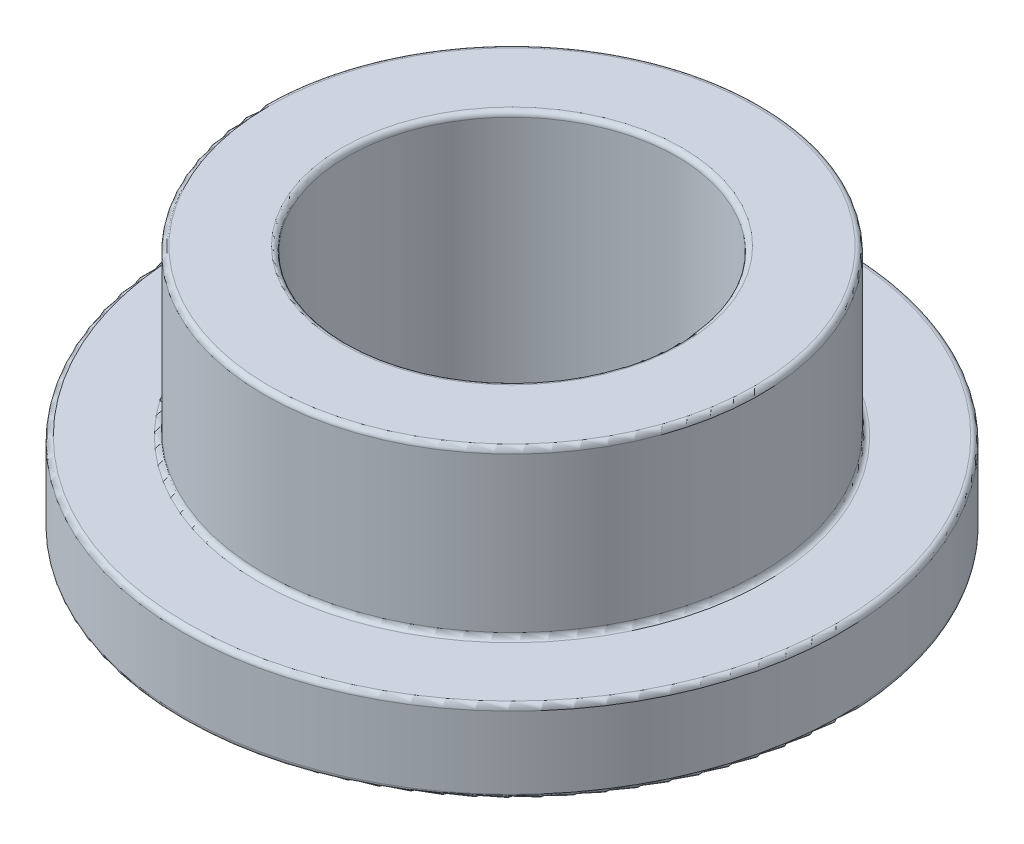
SolidWorks part; units mm, degrees
ref_plane "Front" through (0, 0, 0) normal (0, 0, 1) x (1, 0, 0)
ref_plane "Top" through (0, 0, 0) normal (0, 1, 0) x (1, 0, 0)
ref_plane "Right" through (0, 0, 0) normal (1, 0, 0) x (0, 0, -1)
sketch "Sketch1" plane through (0, 0, 0) normal (0, 1, 0) x (1, 0, 0)
  circle A0 centre (0, 0) radius 4.005
  circle A1 centre (0, 0) radius 6.015
  circle A2 centre (0, 0) radius 8
  dimension "ID" = 8.01
  dimension "OD" = 12.03
  dimension "FlangeOD" = 16
sketch "Sketch2" plane through (0, 0, 0) normal (1, 0, 0) x (0, 0, -1)
  line L0 (8, 0) -> (8, 2) construction
  line L1 (-6.015, 0) -> (-6.015, 6) construction
  line L8 (0, 0) -> (0, 6) construction
  point P5 (-8, 0)
  dimension "Flange Thickness" = 2
  dimension "Length" = 6
sketch "Sketch3" plane through (0, 0, 0) normal (0, 1, 0) x (1, 0, 0)
  circle A0 centre (0, 0) radius 4.005 construction
  circle A1 centre (0, 0) radius 6.015 construction
  circle A2 centre (0, 0) radius 4.005
  circle A3 centre (0, 0) radius 6.015
extrude "Boss-Extrude1" add sketch "Sketch3" along normal up to vertex (6 mm away) up to point (0, 6, 6.015)
sketch "Sketch4" plane through (0, 0, 0) normal (0, 1, 0) x (1, 0, 0)
  circle A0 centre (0, 0) radius 8 construction
  circle A1 centre (0, 0) radius 6.015 construction
  circle A2 centre (0, 0) radius 8
  circle A3 centre (0, 0) radius 6.015
extrude "Boss-Extrude2" add sketch "Sketch4" along normal up to vertex (2 mm away) up to point (0, 2, -8)
fillet "Fillet1" radius 0.125 6 edges at (0, 0, 4.005) (0, 0, 8) (0, 2, 6.015) (0, 2, 8) (0, 6, 4.005) (0, 6, 6.015)
